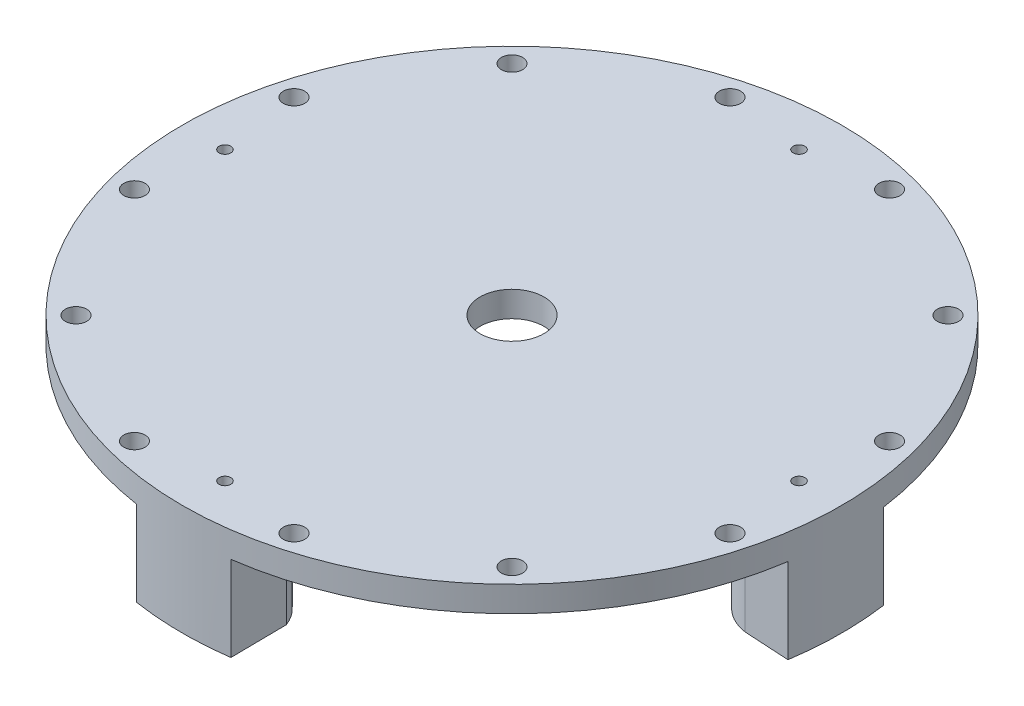
SolidWorks part; units mm, degrees
material "6061-T6 (SS)"
ref_plane "Front Plane" through (0, 0, 0) normal (0, 0, 1) x (1, 0, 0)
ref_plane "Top Plane" through (0, 0, 0) normal (0, 1, 0) x (1, 0, 0)
ref_plane "Right Plane" through (0, 0, 0) normal (1, 0, 0) x (0, 0, -1)
sketch "Sketch1" plane through (0, 0, 0) normal (0, 1, 0) x (1, 0, 0)
  circle A0 centre (0, 0) radius 98.425
  circle A1 centre (0, 0) radius 9.525
  dimension "D1" = 196.85
  dimension "D2" = 19.05
extrude "Boss-Extrude1" add sketch "Sketch1" along normal blind 7.62
sketch "Sketch2" plane through (0, 0, 0) normal (0, -1, 0) x (1, 0, 0)
  line L0 (0, 0) -> (0, 75.6548) construction
  line L1 (13.05, 85.725) -> (0.0025, 85.725) construction
  line L2 (-12.7, 85.725) -> (-1009.5225, 85.725) construction
  line L3 (0, 73.025) -> (0, 50000) construction
  line L4 (-14.0929, 83.7516) -> (-14.8752, 97.2945)
  line L6 (13.5312, 97.4904) -> (13.3337, 80.7532)
  line L13 (83.7516, 14.0929) -> (97.2945, 14.8752)
  line L14 (97.4904, -13.5312) -> (80.7532, -13.3337)
  line L15 (14.0929, -83.7516) -> (14.8752, -97.2945)
  line L16 (-13.5312, -97.4904) -> (-13.3337, -80.7532)
  line L17 (-83.7516, -14.0929) -> (-97.2945, -14.8752)
  line L18 (-97.4904, 13.5312) -> (-80.7532, 13.3337)
  arc A0 (0.1408, 73.0258) -> (0, 73.025) centre (0, 85.725) ccw construction
  circle A1 centre (0, 0) radius 98.425 construction
  arc A10 (-14.0929, 83.7516) -> (13.3337, 80.7532) centre (0, 85.725) ccw
  arc A25 (-14.8752, 97.2945) -> (13.5312, 97.4904) centre (0, 0) cw
  arc A26 (97.2945, 14.8752) -> (97.4904, -13.5312) centre (0, 0) cw
  arc A27 (83.7516, 14.0929) -> (80.7532, -13.3337) centre (85.725, 0) ccw
  arc A28 (14.8752, -97.2945) -> (-13.5312, -97.4904) centre (0, 0) cw
  arc A29 (14.0929, -83.7516) -> (-13.3337, -80.7532) centre (0, -85.725) ccw
  arc A30 (-97.2945, -14.8752) -> (-97.4904, 13.5312) centre (0, 0) cw
  arc A31 (-83.7516, -14.0929) -> (-80.7532, 13.3337) centre (-85.725, 0) ccw
  point P7 (-12.7, 85.725)
  point P8 (12.7, 85.725)
  point P9 (12.2673, 82.438)
  point P13 (0, 93.5788)
  point P17 (-12.2673, 82.438)
  point P26 (12.556, 85.725)
  point P27 (-12.6299, 85.725)
  point P28 (-12.6299, 85.725)
  point P44 (0, 0)
  point P52 (0, 0)
  dimension "D1" = 4
  dimension "D2" = 85.725
extrude "Boss-Extrude2" add sketch "Sketch2" along normal blind 25.4
sketch "Sketch4" plane through (0, 7.62, 0) normal (0, 1, 0) x (1, 0, 0)
  line L0 (0, 0) -> (23.8636, 89.0603) construction
  line L1 (0, 0) -> (0, 98.425) construction
  circle A0 centre (23.8636, 89.0603) radius 3.175
  circle A1 centre (65.1967, 65.1967) radius 3.175
  circle A2 centre (89.0603, 23.8636) radius 3.175
  circle A3 centre (89.0603, -23.8636) radius 3.175
  circle A4 centre (65.1967, -65.1967) radius 3.175
  circle A5 centre (23.8636, -89.0603) radius 3.175
  circle A6 centre (-23.8636, -89.0603) radius 3.175
  circle A7 centre (-65.1967, -65.1967) radius 3.175
  circle A8 centre (-89.0603, -23.8636) radius 3.175
  circle A9 centre (-89.0603, 23.8636) radius 3.175
  circle A10 centre (-65.1967, 65.1967) radius 3.175
  circle A11 centre (-23.8636, 89.0603) radius 3.175
  circle A12 centre (0, 0) radius 98.425 construction
  point P28 (0, 0)
  dimension "D1" = 6.35
  dimension "D3" = 12
  dimension "D2" = 92.202
  dimension "D4" = 15
sketch "Sketch5" plane through (0, -25.4, 0) normal (0, -1, 0) x (1, 0, 0)
  line L0 (200013.05, 85.725) -> (-199999.9975, 85.725) construction
  line L1 (0, 73.025) -> (0, 250000) construction
  line L2 (200013.05, 85.725) -> (-199999.9975, 85.725) construction
  line L3 (0, 73.025) -> (0, 250000) construction
  circle A0 centre (0, 85.725) radius 5.2578
  point P17 (0.7848, -0.7848)
  dimension "D1" = 10.5156
  dimension "D2" = 85.725
extrude "Cut-Extrude3" cut sketch "Sketch5" against normal blind 19.05
sketch "Sketch6" plane through (0, 7.62, 0) normal (0, 1, 0) x (1, 0, 0)
  line L0 (0, 0) -> (0, 98.425) construction
  line L1 (0, 0) -> (-25.4743, 95.0712) construction
  circle A0 centre (0, 0) radius 98.425 construction
  circle A1 centre (-23.8308, 88.9376) radius 3.175
  point P33 (0, 0)
  dimension "D2" = 6.35
  dimension "D1" = 15
  dimension "D3" = 92.075
extrude "Cut-Extrude4" cut sketch "Sketch6" against normal blind 12.7
extrude "Cut-Extrude2" [suppressed] cut sketch "Sketch4" against normal blind 12.7
pattern_circular "CirPattern1" count 12 over 360 about axis through (0, 0, 0) along (0, 1, 0) of "Cut-Extrude4"
pattern_circular "CirPattern2" count 4 over 360 about axis through (0, 0, 0) along (0, 1, 0) of "Cut-Extrude3"
ref_plane "Plane1" through (0, 7.62, 0) normal (0, 1, 0) x (1, 0, 0)
sketch "Sketch8" plane through (0, 7.62, 0) normal (0, 1, 0) x (1, 0, 0)
  circle A0 centre (0, 85.725) radius 1.7526
  dimension "D1" = 3.5052
extrude "Cut-Extrude6" cut sketch "Sketch8" against normal through all
pattern_circular "CirPattern3" count 4 over 360 about axis through (0, 0, 0) along (0, 1, 0) of "Cut-Extrude6"
sketch "Sketch9" plane through (0, 7.62, 0) normal (0, 1, 0) x (1, 0, 0)
  circle A0 centre (0, 0) radius 98.425 construction
  point P0 (0, 85.725)
  point P1 (0, 98.425)
